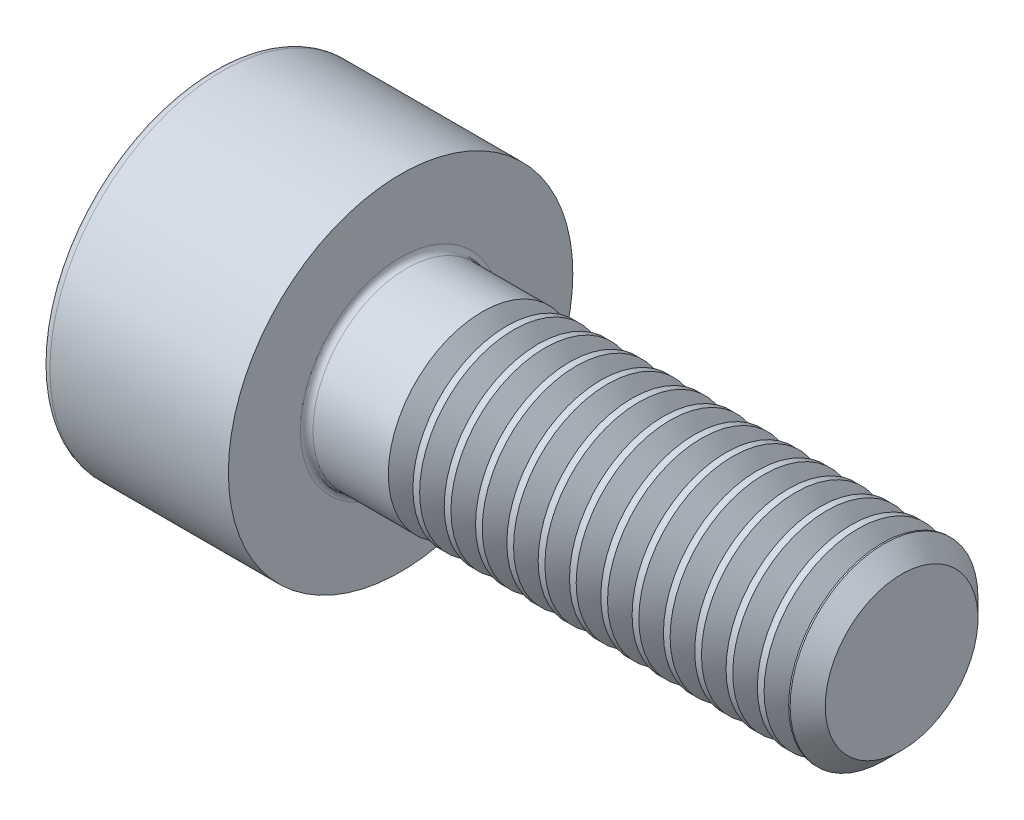
SolidWorks part; units mm, degrees
revolve "Base-Revolve" add sketch "BodySke"
sketch "BodySke" plane through (0, 0, 0) normal (0, 0, 1) x (1, 0, 0)
  line L0 (0, 0) -> (0, 2.75)
  line L1 (0, 2.75) -> (3, 2.75)
  line L2 (3, 2.75) -> (3, 1.5)
  line L3 (3, 1.5) -> (10.7195, 1.5)
  line L4 (11, 1.2195) -> (11, 0)
  line L5 (11, 0) -> (0, 0)
  line L6 (-31.75, 0) -> (127, 0) construction
  line L8 (11, 1.2195) -> (10.7195, 1.5)
  line L10 (11, -1.2195) -> (10.7195, -1.5) construction
  line L11 (3.5, 9.525) -> (3.5, 3.175) construction
  line L12 (3, 9.525) -> (3, 3.175) construction
  line L13 (-49, 9.525) -> (-49, 3.175) construction
  dimension "Head_ht" = 3
  dimension "Length" = 8
  dimension "Body_ch_ang" = 45
  dimension "Diameter" = 3
  dimension "Minor_dia" = 2.439
  dimension "Advance" = 0.5
  dimension "Thread_nom" = 8
  dimension "Thread_length" = 60
  dimension "Head_dia" = 5.5
cosmetic thread "ThreadCosmetic" [suppressed]
fillet "Fillet1" radius 0.1 1 edges at (3, 0, 1.5)
fillet "Fillet2" radius 0.15 1 edges at (0, 0, 2.75)
material "201 Acier inoxydable recuit (SS)"
ref_plane "Plane1" through (0, 0, 0) normal (0, 0, 1) x (1, 0, 0)
ref_plane "Plane2" through (0, 0, 0) normal (0, 1, 0) x (1, 0, 0)
ref_plane "Plane3" through (0, 0, 0) normal (1, 0, 0) x (0, 0, -1)
sketch "Sketch2" plane through (0, 0, 0) normal (0, 0, 1) x (1, 0, 0)
  line L0 (0, 1.28) -> (1.3, 1.28)
  line L1 (1.3, 1.28) -> (2.039, 0)
  line L2 (-31.75, 0) -> (127, 0) construction
  line L3 (2.039, 0) -> (0, 0)
  line L4 (0, 0) -> (0, 1.28)
  line L6 (0, 0) -> (47.625, 0) construction
  dimension "D1" = 1.28
  dimension "D2" = 60
  dimension "Depth" = 1.3
revolve "Hex-PreBroach" cut sketch "Sketch2" angle 360 about L6
sketch "Sketch3" plane through (0, 0, 0) normal (-1, 0, 0) x (0, 0.5, 0.866)
  line L0 (0.739, 1.28) -> (-0.739, 1.28)
  line L1 (-0.739, 1.28) -> (-1.478, 0)
  line L2 (0.739, 1.28) -> (1.478, 0)
  line L3 (0.739, -1.28) -> (1.478, 0)
  line L4 (0.739, -1.28) -> (-0.739, -1.28)
  line L5 (-0.739, -1.28) -> (-1.478, 0)
  dimension "D1" = 1.28
  dimension "D2" = 1.28
  dimension "Hex_size" = 2.56
extrude "Hex" cut sketch "Sketch3" against normal blind 1.3
sketch "ThdSchSke" plane through (0, 0, 0) normal (0, 0, 1) x (1, 0, 0)
  line L0 (4.5, -1.2195) -> (4.3036, -1.5)
  line L1 (4.5, -1.2195) -> (4.6964, -1.5)
  line L2 (4.6964, -1.5) -> (4.6964, -1.875)
  line L3 (-3.175, 0) -> (5.1513, 0) construction
  line L4 (0, 2.6) -> (0, -2.6) construction
  line L5 (4.6964, -1.875) -> (4.3036, -1.875)
  line L6 (4.3036, -1.875) -> (4.3036, -1.5)
  dimension "Thread_minor" = 2.439
  dimension "Diameter" = 3
  dimension "Start" = 4.5
revolve "ThreadSchematic" cut sketch "ThdSchSke" angle 360 about L3
pattern_linear "ThdSchPat" count 13 spacing 0.5 along (1, 0, 0) of "ThreadSchematic"
equation "\"D2@Sketch3\" = \"Hex_size@Sketch3\" / 2"
equation "\"D1@Sketch3\" = \"Hex_size@Sketch3\" / 2"
equation "\"D1@Sketch2\" = \"Hex_size@Sketch3\" / 2"
equation "\"Thread_minor@ThreadCosmetic\"  =  \"Minor_dia@BodySke\""
equation "\"Depth@Sketch2\" =  \"Key_eng@Hex\""
equation "\"Thread_length@ThreadCosmetic\" = ((sgn( (\"Length@BodySke\" - \"Advance@BodySke\" * 3.0) - \"Thread_nom@BodySke\" )-1)*( (\"Length@BodySke\" - \"Advance@BodySke\" * 3.0) - \"Thread_nom@BodySke\" ))/-2+ \"Thread_nom@BodySke\""
equation "\"Thread_minor@ThdSchSke\" = \"Minor_dia@BodySke\""
equation "\"Diameter@ThdSchSke\" = \"Diameter@BodySke\""
equation "\"Overcut@ThdSchSke\" = \"Diameter@BodySke\" * 1.25"
equation "\"Start@ThdSchSke\" = \"Head_ht@BodySke\" + \"Length@BodySke\" - \"Thread_length@ThreadCosmetic\"  '---Non-countersunk---"
equation "\"Num_threads@ThdSchPat\" = int( \"Thread_length@ThreadCosmetic\" / \"Advance@BodySke\" + 0.999 )  + 1"
equation "\"Advance@ThdSchPat\" = \"Thread_length@ThreadCosmetic\" /  (\"Num_threads@ThdSchPat\" - 1) 'relax it"
equation "\"Num_threads@ThdSchPat\" = \"Num_threads@ThdSchPat\" - sgn( \"Num_threads@ThdSchPat\" - 1) '---chamfered tips only---"
